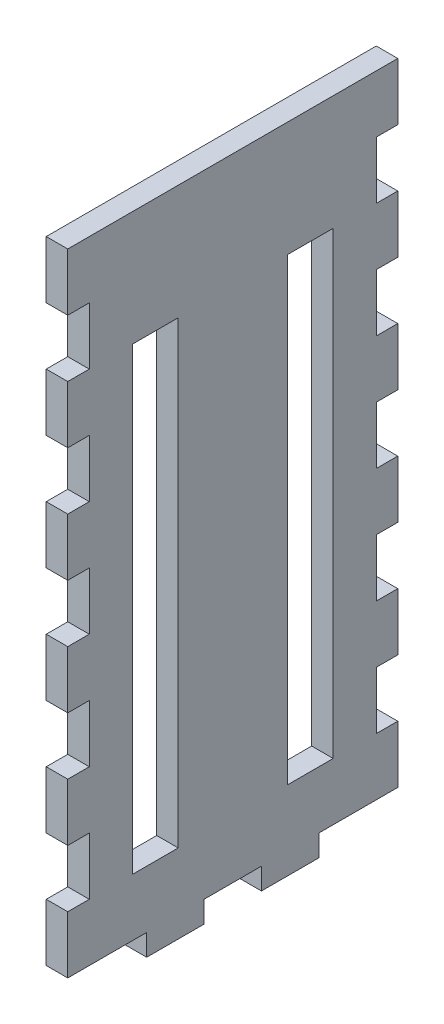
SolidWorks part; units mm, degrees
ref_plane "Front Plane" through (0, 0, 0) normal (0, 0, 1) x (1, 0, 0)
ref_plane "Top Plane" through (0, 0, 0) normal (0, 1, 0) x (1, 0, 0)
ref_plane "Right Plane" through (0, 0, 0) normal (1, 0, 0) x (0, 0, -1)
sketch "Sketch1" plane through (0, 0, 0) normal (1, 0, 0) x (0, 0, -1)
  line L1 (-63.5, -139.7) -> (63.5, -139.7)
  line L2 (-63.5, -139.7) -> (-63.5, 139.7)
  line L3 (-63.5, 139.7) -> (63.5, 139.7)
  line L4 (63.5, -139.7) -> (63.5, 139.7)
  line L5 (-63.5, -139.7) -> (63.5, 139.7) construction
  line L6 (-63.5, 139.7) -> (63.5, -139.7) construction
  point P0 (0, 0)
  dimension "D1" = 127
  dimension "D2" = 279.4
extrude "Boss-Extrude1" add sketch "Sketch1" along normal blind 9.525
sketch "Sketch2" plane through (0, 0, 63.5) normal (0, 0, 1) x (1, 0, 0)
  line L0 (0, 139.7) -> (0, -139.7) construction
  line L1 (0, 139.7) -> (9.525, 139.7)
  line L2 (0, 139.7) -> (0, 114.3)
  line L3 (0, 114.3) -> (9.525, 114.3)
  line L4 (9.525, 139.7) -> (9.525, 114.3)
  line L5 (0, -69.85) -> (0, 69.85) construction
  line L6 (9.525, 139.7) -> (9.525, -139.7) construction
  line L7 (9.525, 139.7) -> (0, 139.7) construction
  dimension "D1" = 25.4
  dimension "D2" = 0
extrude "Boss-Extrude2" add sketch "Sketch2" along normal blind 9.525
pattern_linear "LPattern1" count 6 spacing 50.8 along (0, -1, 0) of "Boss-Extrude2"
mirror "Mirror1" about plane through (0, 0, 0) normal (0, 0, 1) of "LPattern1", "Boss-Extrude2"
sketch "Sketch3" plane through (0, -139.7, 0) normal (0, -1, 0) x (1, 0, 0)
  line L0 (0, 73.025) -> (0, -73.025) construction
  line L1 (0, 38.1) -> (9.525, 38.1)
  line L2 (0, 38.1) -> (0, 12.7)
  line L3 (0, 12.7) -> (9.525, 12.7)
  line L4 (9.525, 38.1) -> (9.525, 12.7)
  line L5 (9.525, 73.025) -> (9.525, -73.025) construction
  line L6 (0, 73.025) -> (9.525, 73.025) construction
  dimension "D1" = 34.925
  dimension "D2" = 25.4
extrude "Boss-Extrude3" add sketch "Sketch3" along normal blind 9.525
pattern_linear "LPattern2" count 2 spacing 50.8 along (0, 0, -1) of "Boss-Extrude3"
sketch "Sketch4" plane through (9.525, 0, 0) normal (1, 0, 0) x (0, 0, -1)
  line L1 (-44.45, -114.3) -> (-24.13, -114.3)
  line L3 (-44.45, 88.9) -> (-24.13, 88.9)
  line L5 (-73.025, -139.7) -> (-38.1, -139.7) construction
  line L6 (-73.025, 88.9) -> (-63.5, 88.9) construction
  line L7 (-24.13, -114.3) -> (-24.13, 88.9)
  line L8 (-44.45, -114.3) -> (-44.45, 88.9)
  line L9 (0, -139.7) -> (0, 139.7) construction
  line L10 (-12.7, -139.7) -> (12.7, -139.7) construction
  line L11 (73.025, 139.7) -> (-73.025, 139.7) construction
  point P10 (-68.2625, 88.9)
  dimension "D1" = 24.13
  dimension "D2" = 20.32
  dimension "D3" = 25.4
  dimension "D4" = 0
extrude "Cut-Extrude1" cut sketch "Sketch4" against normal blind 9.525
mirror "Mirror2" about plane through (0, 0, 0) normal (0, 0, 1) of "Cut-Extrude1"
sketch "Sketch5" plane through (0, 0, 0) normal (-1, 0, 0) x (0, 0, 1)
  circle A0 centre (-1.775, 53.4971) radius 2.5 construction
  circle A1 centre (-1.775, 53.4971) radius 2.5
  circle A2 centre (-1.775, 34.9971) radius 2.5 construction
  circle A3 centre (-1.775, 34.9971) radius 2.5
  circle A4 centre (1.775, 19.4611) radius 2.5 construction
  circle A5 centre (1.775, 19.4611) radius 2.5
  circle A6 centre (1.775, 0.9611) radius 2.5 construction
  circle A7 centre (1.775, 0.9611) radius 2.5
  circle A8 centre (-1.775, -16.5748) radius 2.5 construction
  circle A9 centre (-1.775, -16.5748) radius 2.5
  circle A10 centre (-1.775, -35.0748) radius 2.5 construction
  circle A11 centre (-1.775, -35.0748) radius 2.5
  circle A12 centre (1.775, -50.3148) radius 2.5 construction
  circle A13 centre (1.775, -50.3148) radius 2.5
  circle A14 centre (1.775, -68.8148) radius 2.5 construction
  circle A15 centre (1.775, -68.8148) radius 2.5
